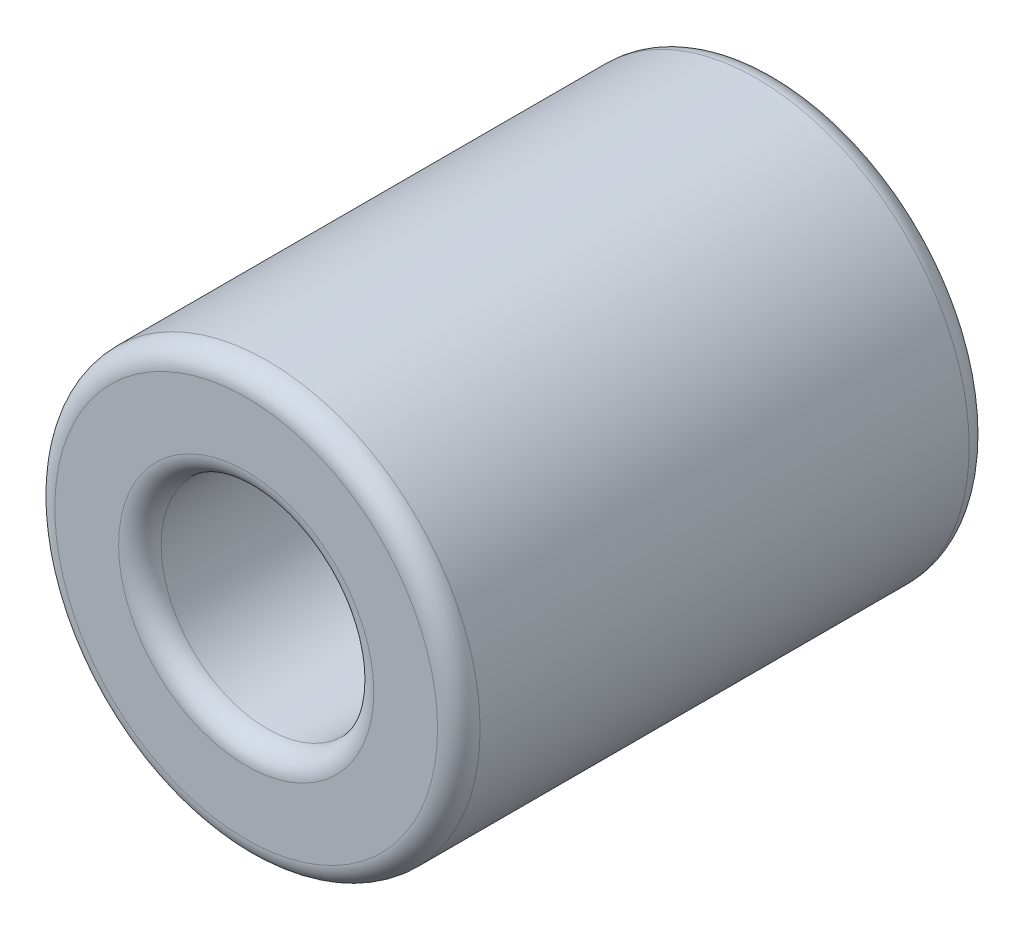
SolidWorks part; units mm, degrees
material "5052-O，棒材(SS)"
ref_plane "前视基准面" through (0, 0, 0) normal (0, 0, 1) x (1, 0, 0)
ref_plane "上视基准面" through (0, 0, 0) normal (0, 1, 0) x (1, 0, 0)
ref_plane "右视基准面" through (0, 0, 0) normal (1, 0, 0) x (0, 0, -1)
sketch "草图1" plane through (0, 0, 0) normal (0, 0, 1) x (1, 0, 0)
  circle A0 centre (0, 0) radius 10
  circle A1 centre (0, 0) radius 5
  dimension "D1" = 20
  dimension "D2" = 10
extrude "凸台-拉伸1" add sketch "草图1" along normal blind 25
fillet "圆角1" radius 1 4 edges at (5, 0, 0) (10, 0, 0) (5, 0, 25) (10, 0, 25)
ref_plane "基准面1" through (0, 0, 10) normal (0, 0, -1) x (-1, 0, 0)
sketch "草图2" plane through (0, 0, 10) normal (0, 0, -1) x (-1, 0, 0)
  circle A0 centre (0, 0) radius 6.969
extrude "凸台-拉伸2" add sketch "草图2" against normal blind 5
